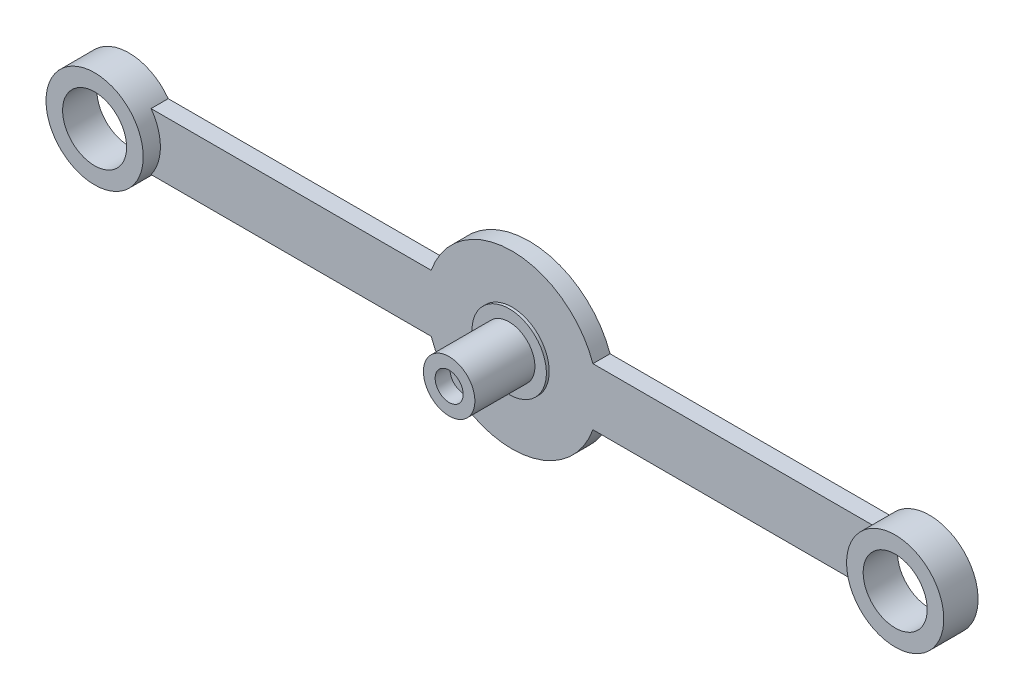
SolidWorks part; units mm, degrees
ref_plane "Front Plane" through (0, 0, 0) normal (0, 0, 1) x (1, 0, 0)
ref_plane "Top Plane" through (0, 0, 0) normal (0, 1, 0) x (1, 0, 0)
ref_plane "Right Plane" through (0, 0, 0) normal (1, 0, 0) x (0, 0, -1)
sketch "Sketch1" plane through (0, 0, 0) normal (0, 0, 1) x (1, 0, 0)
  circle A0 centre (0, 0) radius 4.5
  dimension "D1" = 9
extrude "Boss-Extrude1" add sketch "Sketch1" along normal blind 11
sketch "Sketch2" plane through (0, 0, 0) normal (0, 0, 1) x (1, 0, 0)
  line L1 (0, 0) -> (70, 0) construction
  line L2 (0, 5) -> (70, 5) construction
  line L4 (14.1421, 5) -> (63.1261, 5)
  line L5 (14.1421, -5) -> (63.1261, -5)
  line L6 (0, 15) -> (0, -15.6367) construction
  line L7 (-14.1421, -5) -> (-63.1261, -5)
  line L8 (-14.1421, 5) -> (-63.1261, 5)
  circle A4 centre (70, 0) radius 5.6
  circle A10 centre (0, 0) radius 15 construction
  circle A11 centre (70, 0) radius 8.5 construction
  arc A12 (-14.1421, 5) -> (14.1421, 5) centre (0, 0) cw
  arc A13 (63.1261, -5) -> (63.1261, 5) centre (70, 0) ccw
  arc A14 (-14.1421, -5) -> (14.1421, -5) centre (0, 0) ccw
  circle A15 centre (-70, 0) radius 5.6
  arc A16 (-63.1261, -5) -> (-63.1261, 5) centre (-70, 0) cw
  dimension "D1" = 11.2
  dimension "D2" = 70
  dimension "D3" = 5
  dimension "D4" = 30
  dimension "D5" = 17
extrude "Boss-Extrude2" add sketch "Sketch2" against normal blind 3
sketch "Sketch3" plane through (0, 0, 0) normal (0, 0, 1) x (1, 0, 0)
  circle A0 centre (0, 0) radius 6.5
  dimension "D1" = 13
extrude "Boss-Extrude3" add sketch "Sketch3" along normal blind 0.5 from surface at 0 starting at face at (4.5, 0, 0)
sketch "Sketch4" plane through (0, 0, 0) normal (0, 0, 1) x (1, 0, 0)
  circle A0 centre (-70, 0) radius 5.6
  circle A1 centre (-70, 0) radius 8.5
  circle A2 centre (70, 0) radius 5.6
  circle A3 centre (70, 0) radius 8.5
extrude "Boss-Extrude4" add sketch "Sketch4" along normal blind 3 from surface at 0 starting at face at (-6.5, 0, 0)
sketch "Sketch5" plane through (0, 0, 0) normal (0, 0, 1) x (1, 0, 0)
  circle A0 centre (0, 0) radius 2.45
  dimension "D1" = 4.9
extrude "Cut-Extrude1" cut sketch "Sketch5" against normal offset from surface (2.6 mm away) 8.4 from surface at 11 up to face at (-6.5, 0, 0) starting at face at (4.5, 0, 11)
sketch "Sketch7" plane through (0, 0, 0) normal (0, 0, 1) x (1, 0, 0)
  circle A0 centre (0, 0) radius 1.2
  dimension "D1" = 2.4
extrude "Cut-Extrude3" cut sketch "Sketch7" against normal through all both and the other way through all
sketch "Sketch8" plane through (0, 0, 0) normal (0, 0, 1) x (1, 0, 0)
  circle A0 centre (0, 0) radius 2.7
  dimension "D1" = 5.4
extrude "Cut-Extrude4" cut sketch "Sketch8" along normal offset from surface (8.9 mm away) 2.5 from surface at -3 up to face at (-1.2, 0, 8.4) starting at face at (1.2, 0, -3)
sketch "Sketch9" plane through (0, 0, 0) normal (0, 0, 1) x (1, 0, 0)
  circle A0 centre (0, 0) radius 12.101
  circle A1 centre (0, 0) radius 85.7929
  point P4 (0, 0)
extrude "Cut-Extrude5" [suppressed] cut sketch "Sketch9" against normal through all both and the other way through all
